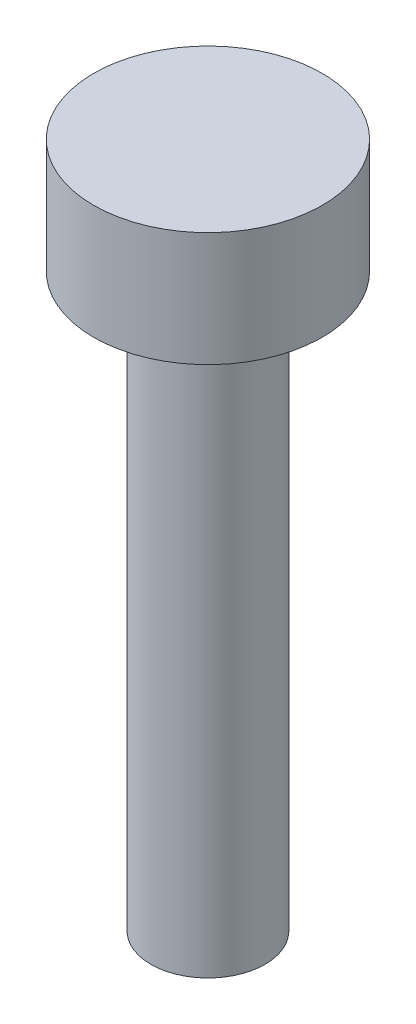
SolidWorks part; units mm, degrees
ref_plane "Front Plane" through (0, 0, 0) normal (0, 0, 1) x (1, 0, 0)
ref_plane "Top Plane" through (0, 0, 0) normal (0, 1, 0) x (1, 0, 0)
ref_plane "Right Plane" through (0, 0, 0) normal (1, 0, 0) x (0, 0, -1)
sketch "Sketch1" plane through (0, 0, 0) normal (0, 1, 0) x (1, 0, 0)
  circle A0 centre (0, 0) radius 1.27
  dimension "D1" = 2.54
extrude "Boss-Extrude1" add sketch "Sketch1" along normal blind 12.7
sketch "Sketch2" plane through (0, 12.7, 0) normal (0, 1, 0) x (1, 0, 0)
  circle A0 centre (0, 0) radius 2.54
  dimension "D1" = 5.08
extrude "Boss-Extrude2" add sketch "Sketch2" along normal blind 2.54
